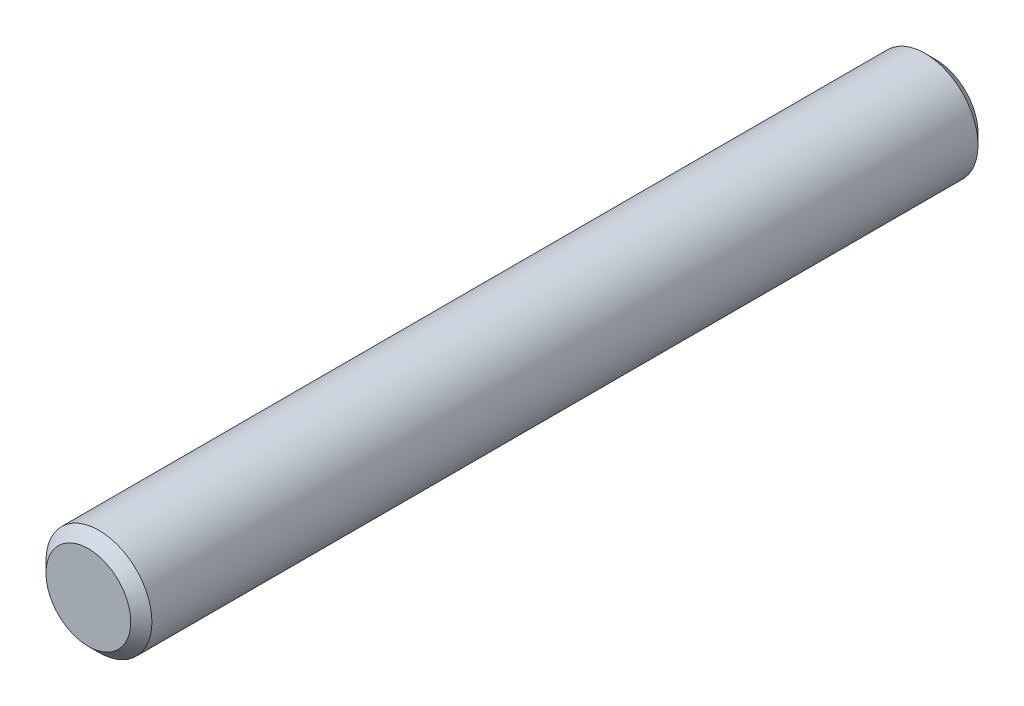
SolidWorks part; units mm, degrees
material "Alloy Steel"
ref_plane "Front Plane" through (0, 0, 0) normal (0, 0, 1) x (1, 0, 0)
ref_plane "Top Plane" through (0, 0, 0) normal (0, 1, 0) x (1, 0, 0)
ref_plane "Right Plane" through (0, 0, 0) normal (1, 0, 0) x (0, 0, -1)
sketch "Sketch1" plane through (0, 0, 0) normal (0, 1, 0) x (1, 0, 0)
  line L0 (1.2, 12) -> (0, 12)
  line L1 (0, 12) -> (0, -12)
  line L2 (0, -12) -> (1.2, -12)
  line L3 (1.2, -12) -> (1.5, -11.7)
  line L4 (1.5, -11.7) -> (1.5, 11.7)
  line L5 (1.5, 11.7) -> (1.2, 12)
  line L6 (0, 12) -> (0, -12) construction
revolve "Revolve1" add sketch "Sketch1" angle 360 about L6
